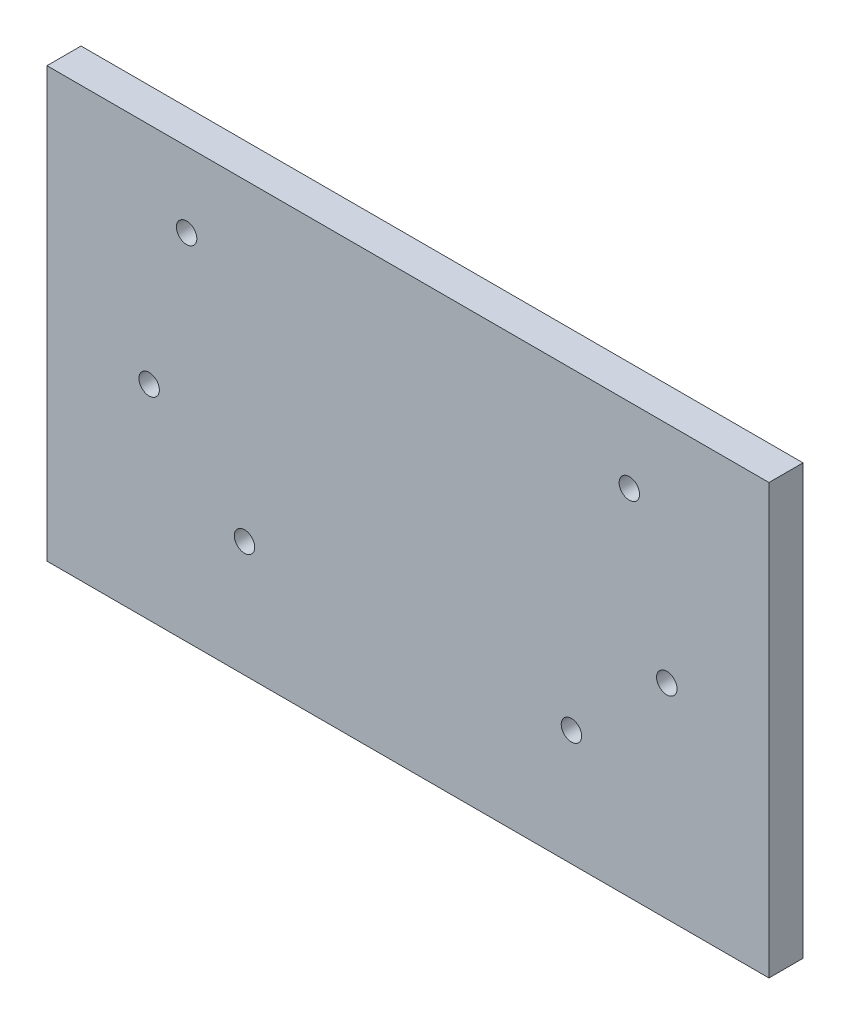
SolidWorks part; units mm, degrees
ref_plane "Front" through (0, 0, 0) normal (0, 0, 1) x (1, 0, 0)
ref_plane "Top" through (0, 0, 0) normal (0, 1, 0) x (1, 0, 0)
ref_plane "Right" through (0, 0, 0) normal (1, 0, 0) x (0, 0, -1)
sketch "Sketch1" plane through (0, 0, 0) normal (0, 0, 1) x (1, 0, 0)
  line L1 (-53, 31.5) -> (53, 31.5)
  line L2 (-53, 31.5) -> (-53, -31.5)
  line L3 (-53, -31.5) -> (53, -31.5)
  line L4 (53, 31.5) -> (53, -31.5)
  line L5 (-53, 31.5) -> (53, -31.5) construction
  line L6 (-53, -31.5) -> (53, 31.5) construction
  point P0 (0, 0)
  dimension "D1" = 63
  dimension "D2" = 106
extrude "Boss-Extrude1" add sketch "Sketch1" along normal blind 5
sketch "Sketch2" plane through (0, 0, 0) normal (0, 0, 1) x (1, 0, 0)
  line L0 (-53, -31.5) -> (53, -31.5) construction
  line L1 (0, 31.5) -> (0, -31.5) construction
  line L2 (53, 31.5) -> (-53, 31.5) construction
  circle A0 centre (-24, -14.5) radius 1.5
  circle A1 centre (24, -14.5) radius 1.5
  circle A2 centre (-38, -1.5) radius 1.5
  circle A3 centre (38, -1.5) radius 1.5
  circle A4 centre (-32.5, 20.5) radius 1.5
  circle A5 centre (32.5, 20.5) radius 1.5
  dimension "D1" = 3
  dimension "D2" = 3
  dimension "D6" = 3
  dimension "D7" = 3
  dimension "D11" = 3
  dimension "D12" = 3
  dimension "D3" = 17
  dimension "D4" = 48
  dimension "D5" = 24
  dimension "D8" = 76
  dimension "D9" = 38
  dimension "D10" = 30
  dimension "D13" = 11
  dimension "D14" = 65
  dimension "D15" = 32.5
extrude "Cut-Extrude2" cut sketch "Sketch2" along normal through all
ref_plane "Plane1" through (0, -31.5, 0) normal (0, -1, 0) x (-1, 0, 0)
equation "\"D5@Sketch2\"= \"D4@Sketch2\" / 2"
equation "\"D9@Sketch2\"= \"D8@Sketch2\" / 2"
equation "\"D15@Sketch2\"= \"D14@Sketch2\" / 2"
